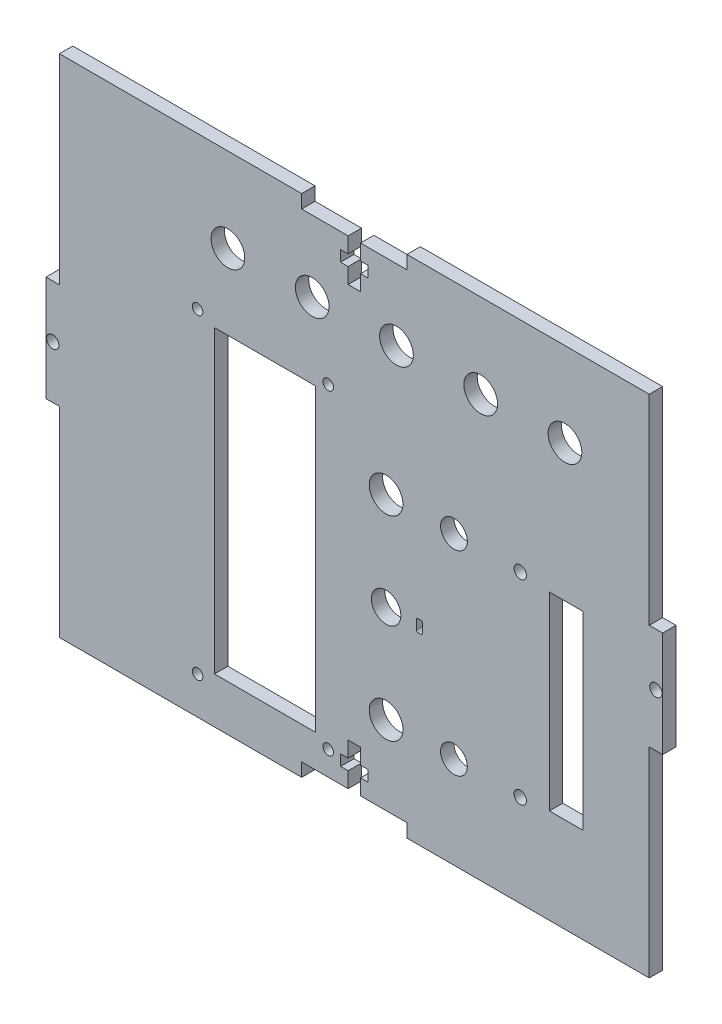
SolidWorks part; units mm, degrees
ref_plane "Front Plane" through (0, 0, 0) normal (0, 0, 1) x (1, 0, 0)
ref_plane "Top Plane" through (0, 0, 0) normal (0, 1, 0) x (1, 0, 0)
ref_plane "Right Plane" through (0, 0, 0) normal (1, 0, 0) x (0, 0, -1)
sketch "Sketch1" plane through (0, 0, 0) normal (0, 0, 1) x (1, 0, 0)
  line L0 (0, 60) -> (0, -60) construction
  line L1 (-70, 60) -> (70, 60)
  line L2 (-70, 60) -> (-70, -60)
  line L3 (-70, -60) -> (70, -60)
  line L4 (70, 60) -> (70, -60)
  line L5 (-70, 60) -> (70, -60) construction
  line L6 (-70, -60) -> (70, 60) construction
  line L7 (-70, 0) -> (70, 0) construction
  line L8 (-3.25, -50.525) -> (3.25, -50.525)
  line L9 (12.5, 60) -> (-12.5, 60)
  line L10 (12.5, 60) -> (12.5, 56.825)
  line L11 (12.5, 56.825) -> (-12.5, 56.825)
  line L12 (-12.5, 60) -> (-12.5, 56.825)
  line L13 (12.5, 60) -> (-12.5, 56.825) construction
  line L14 (12.5, 56.825) -> (-12.5, 60) construction
  line L15 (-1.47, 56.825) -> (1.47, 56.825)
  line L16 (-1.47, 56.825) -> (-1.47, 46.825)
  line L17 (-1.47, 46.825) -> (1.47, 46.825)
  line L18 (1.47, 56.825) -> (1.47, 46.825)
  line L19 (-1.47, 56.825) -> (1.47, 46.825) construction
  line L20 (-1.47, 46.825) -> (1.47, 56.825) construction
  line L21 (-3.25, 53.125) -> (3.25, 53.125)
  line L22 (-3.25, 53.125) -> (-3.25, 50.525)
  line L23 (-3.25, 50.525) -> (3.25, 50.525)
  line L24 (3.25, 53.125) -> (3.25, 50.525)
  line L25 (-3.25, 53.125) -> (3.25, 50.525) construction
  line L26 (-3.25, 50.525) -> (3.25, 53.125) construction
  line L27 (3.25, -53.125) -> (3.25, -50.525)
  line L28 (-3.25, -53.125) -> (3.25, -53.125)
  line L29 (-3.25, -53.125) -> (-3.25, -50.525)
  line L30 (-1.47, -46.825) -> (1.47, -46.825)
  line L31 (1.47, -56.825) -> (1.47, -46.825)
  line L32 (-1.47, -56.825) -> (1.47, -56.825)
  line L33 (-1.47, -56.825) -> (-1.47, -46.825)
  line L34 (12.5, -56.825) -> (-12.5, -56.825)
  line L35 (-12.5, -60) -> (-12.5, -56.825)
  line L36 (12.5, -60) -> (-12.5, -60)
  line L37 (12.5, -60) -> (12.5, -56.825)
  line L38 (73.175, -12.5) -> (70, -12.5)
  line L39 (-73.175, 12.5) -> (-70, 12.5)
  line L40 (-73.175, 12.5) -> (-73.175, -12.5)
  line L41 (-73.175, -12.5) -> (-70, -12.5)
  line L42 (-70, 12.5) -> (-70, -12.5)
  line L43 (-73.175, 12.5) -> (-70, -12.5) construction
  line L44 (-73.175, -12.5) -> (-70, 12.5) construction
  line L45 (70, 12.5) -> (70, -12.5)
  line L46 (73.175, 12.5) -> (70, 12.5)
  line L47 (73.175, 12.5) -> (73.175, -12.5)
  circle A0 centre (-71.5875, 0) radius 1.47
  circle A1 centre (71.5875, 0) radius 1.47
  point P0 (0, 0)
  point P10 (0, 58.4125)
  point P15 (0, 51.825)
  point P20 (0, 51.825)
  point P37 (-71.5875, 0)
  dimension "D11" = 2.94
  dimension "D1" = 120
  dimension "D2" = 140
  dimension "D3" = 3.175
  dimension "D4" = 10
  dimension "D5" = 2.94
  dimension "D6" = 25
  dimension "D7" = 6.5
  dimension "D8" = 2.6
  dimension "D9" = 6.3
  dimension "D10" = 3.175
extrude "Boss-Extrude1" add sketch "Sketch1" along normal mid plane 3.175 contours L21 L24 L23 L18 L17 L16 L22 L11 L12 L1 L2 L3 L4 L10 | L40 L39 L42 L41 | A0 | L38 L45 L46 L47 | A1
sketch "Sketch3" plane through (0, 0, -1.5875) normal (0, 0, -1) x (-1, 0, 0)
  line L0 (-9.6476, 0) -> (-9.6476, -15) construction
  line L5 (-9.6476, -15) -> (-19.2951, -15) construction
  line L6 (-50.3, 7.5) -> (-50.3, -22.5) construction
  line L7 (-46.3, 7.5) -> (-54.3, 7.5)
  line L8 (-46.3, 7.5) -> (-46.3, -37.5)
  line L9 (-46.3, -37.5) -> (-54.3, -37.5)
  line L10 (-54.3, 7.5) -> (-54.3, -37.5)
  line L11 (-48.7125, -40) -> (-48.7125, 10) construction
  line L12 (-51.8875, 10) -> (-51.8875, -40) construction
  line L13 (0, 0) -> (-19.2951, 0) construction
  dimension "D1" = 8
  dimension "D2" = 45
  dimension "D3" = 15
extrude "Cut-Extrude1" cut sketch "Sketch3" against normal through all
sketch "Sketch4" plane through (0, 0, -1.5875) normal (0, 0, -1) x (-1, 0, 0)
  line L0 (33.2, 21.2555) -> (33.2, -48.2445) construction
  line L1 (33.2, 22.1055) -> (9.2, 22.1055)
  line L2 (33.2, 22.1055) -> (33.2, -49.0945)
  line L3 (33.2, -49.0945) -> (9.2, -49.0945)
  line L4 (9.2, 22.1055) -> (9.2, -49.0945)
  line L5 (9.2, -48.2445) -> (9.2, 21.2555) construction
  line L6 (10.05, 22.1055) -> (16.7, 22.1055) construction
  line L7 (32.35, -49.0945) -> (10.05, -49.0945) construction
extrude "Cut-Extrude2" cut sketch "Sketch4" against normal through all
sketch "Sketch5" plane through (0, 0, -1.5875) normal (0, 0, -1) x (-1, 0, 0)
  line L0 (-15.1534, -16.25) -> (-15.7792, -16.25) construction
  line L1 (-15.7792, -13.75) -> (-15.1534, -13.75) construction
  line L2 (-14.9534, -13.95) -> (-14.9534, -16.05) construction
  line L3 (-15.1534, -16.25) -> (-15.7792, -16.25)
  line L4 (-15.7792, -13.75) -> (-15.1534, -13.75)
  line L5 (-14.9534, -13.95) -> (-14.9534, -16.05)
  line L6 (-15.1534, -16.45) -> (-15.7792, -16.45)
  line L7 (-15.7792, -13.55) -> (-15.1534, -13.55)
  line L8 (-14.7534, -13.95) -> (-14.7534, -16.05)
  arc A0 (-15.1534, -16.25) -> (-14.9534, -16.05) centre (-15.1534, -16.05) ccw construction
  arc A1 (-15.9775, -16.0753) -> (-15.7792, -16.25) centre (-15.7792, -16.05) ccw construction
  arc A2 (-15.9775, -13.9247) -> (-15.9775, -16.0753) centre (-7.5458, -15) ccw construction
  arc A3 (-15.7792, -13.75) -> (-15.9775, -13.9247) centre (-15.7792, -13.95) ccw construction
  arc A4 (-14.9534, -13.95) -> (-15.1534, -13.75) centre (-15.1534, -13.95) ccw construction
  arc A5 (-15.1534, -16.25) -> (-14.9534, -16.05) centre (-15.1534, -16.05) ccw
  arc A6 (-15.9775, -16.0753) -> (-15.7792, -16.25) centre (-15.7792, -16.05) ccw
  arc A7 (-15.9775, -13.9247) -> (-15.9775, -16.0753) centre (-7.5458, -15) ccw
  arc A8 (-15.7792, -13.75) -> (-15.9775, -13.9247) centre (-15.7792, -13.95) ccw
  arc A9 (-14.9534, -13.95) -> (-15.1534, -13.75) centre (-15.1534, -13.95) ccw
  arc A10 (-16.1759, -16.1006) -> (-15.7792, -16.45) centre (-15.7792, -16.05) ccw
  arc A11 (-16.1759, -13.8994) -> (-16.1759, -16.1006) centre (-7.5458, -15) ccw
  arc A12 (-15.7792, -13.55) -> (-16.1759, -13.8994) centre (-15.7792, -13.95) ccw
  arc A13 (-14.7534, -13.95) -> (-15.1534, -13.55) centre (-15.1534, -13.95) ccw
  arc A14 (-15.1534, -16.45) -> (-14.7534, -16.05) centre (-15.1534, -16.05) ccw
  dimension "D1" = 0.2
extrude "Cut-Extrude4" cut sketch "Sketch5" against normal through all contours L8 A14 L6 A10 A11 A12 L7 A13
sketch "Sketch6" plane through (0, 0, -1.5875) normal (0, 0, -1) x (-1, 0, 0)
  line L0 (-70, 40) -> (70, 40) construction
  line L1 (-70, 56.825) -> (-70, 12.5) construction
  line L2 (70, 60) -> (70, 12.5) construction
  line L3 (70, 60) -> (12.5, 60) construction
  line L4 (-50, 40) -> (-30, 40)
  line L5 (-30, 40) -> (-10, 40)
  line L6 (-10, 40) -> (10, 40)
  line L7 (10, 40) -> (30, 40)
  line L8 (-70, 60) -> (-70, 12.5) construction
  line L9 (-10, 40) -> (10, 40)
  line L10 (-30, 40) -> (-10, 40)
  line L11 (-50, 40) -> (-30, 40)
  line L12 (-70, 40) -> (-50, 40)
  circle A0 centre (30, 40) radius 4
  circle A1 centre (10, 40) radius 4
  circle A2 centre (-10, 40) radius 4
  circle A3 centre (-30, 40) radius 4
  circle A4 centre (-50, 40) radius 4
  dimension "D4" = 8
  dimension "D1" = 20
  dimension "D2" = 20
  dimension "D3" = 20
  dimension "D5" = 5
extrude "Cut-Extrude5" cut sketch "Sketch6" against normal through all contours A0 | A1 | A2 | A3 | A4
sketch "Sketch9" plane through (0, 0, 1.5875) normal (0, 0, 1) x (1, 0, 0)
  circle A0 centre (-37.2, 23.9055) radius 1.25 construction
  circle A1 centre (-6.2, 23.9055) radius 1.25 construction
  circle A2 centre (-6.2, -51.0945) radius 1.25 construction
  circle A3 centre (-37.2, -51.0945) radius 1.25 construction
  circle A4 centre (-37.2, 23.9055) radius 1.25
  circle A5 centre (-6.2, 23.9055) radius 1.25
  circle A6 centre (-6.2, -51.0945) radius 1.25
  circle A7 centre (-37.2, -51.0945) radius 1.25
  circle A8 centre (39.3875, 8.1613) radius 1.47 construction
  circle A9 centre (39.3875, -38.1613) radius 1.47 construction
  circle A10 centre (39.3875, 8.1613) radius 1.47
  circle A11 centre (39.3875, -38.1613) radius 1.47
extrude "Cut-Extrude6" cut sketch "Sketch9" against normal through all
sketch "Sketch10" plane through (0, 0, -1.5875) normal (0, 0, -1) x (-1, 0, 0)
  line L1 (-23.65, 8.1613) -> (-37.9175, 8.1613) construction
  line L2 (-23.65, -38.1613) -> (-37.9175, -38.1613) construction
  line L3 (-33.65, 28.1613) -> (-33.65, -11.8387) construction
  line L4 (50, 60) -> (50, -60) construction
  line L5 (70, 60) -> (12.5, 60) construction
  line L6 (70, -60) -> (12.5, -60) construction
  line L7 (70, 60) -> (70, 12.5) construction
  line L8 (-33.65, -18.1613) -> (-33.65, -58.1613) construction
  line L9 (-23.65, 8.1613) -> (-16.825, 8.1613) construction
  line L10 (-16.825, 28.1613) -> (-16.825, -11.8387) construction
  line L11 (-23.65, -38.1613) -> (-16.825, -38.1613) construction
  line L12 (-16.825, -18.1613) -> (-16.825, -58.1613) construction
  circle A0 centre (-39.3875, 8.1613) radius 1.47 construction
  circle A1 centre (-39.3875, -38.1613) radius 1.47 construction
  point P28 (0, 0)
  dimension "D1" = 20
  dimension "D2" = 10
  dimension "D3" = 6.825
  dimension "D4" = 40
  dimension "D5" = 40
  dimension "D6" = 6.825
  dimension "D7" = 10
  dimension "D8" = 40
  dimension "D9" = 40
sketch "Sketch11" plane through (0, 0, -1.5875) normal (0, 0, -1) x (-1, 0, 0)
  text T0 "Alden Dent PID Box" font "Century Gothic" height 9
  text T1 "Power Off" font "Century Gothic" height 3.175
  text T2 "PID Off" font "Century Gothic" height 3.175
  text T3 "Power On" font "Century Gothic" height 3.175
  text T4 "PID On" font "Century Gothic" height 3.175
sketch "Sketch12" plane through (0, 0, -1.5875) normal (0, 0, -1) x (-1, 0, 0)
  circle A1 centre (-7.5458, -38.1613) radius 4
  circle A2 centre (-7.5458, 8.1613) radius 4
  circle A3 centre (-7.5458, -15) radius 3.5
  arc A6 (-21.105, 10.0596) -> (-21.105, 6.2629) centre (-23.65, 8.1613) ccw construction
  circle A10 centre (-23.65, -38.1613) radius 3.175
  circle A11 centre (-23.65, 8.1613) radius 3.175
  dimension "D1" = 7
  dimension "D2" = 8
  dimension "D3" = 6.35
extrude "Cut-Extrude7" cut sketch "Sketch12" against normal through all
